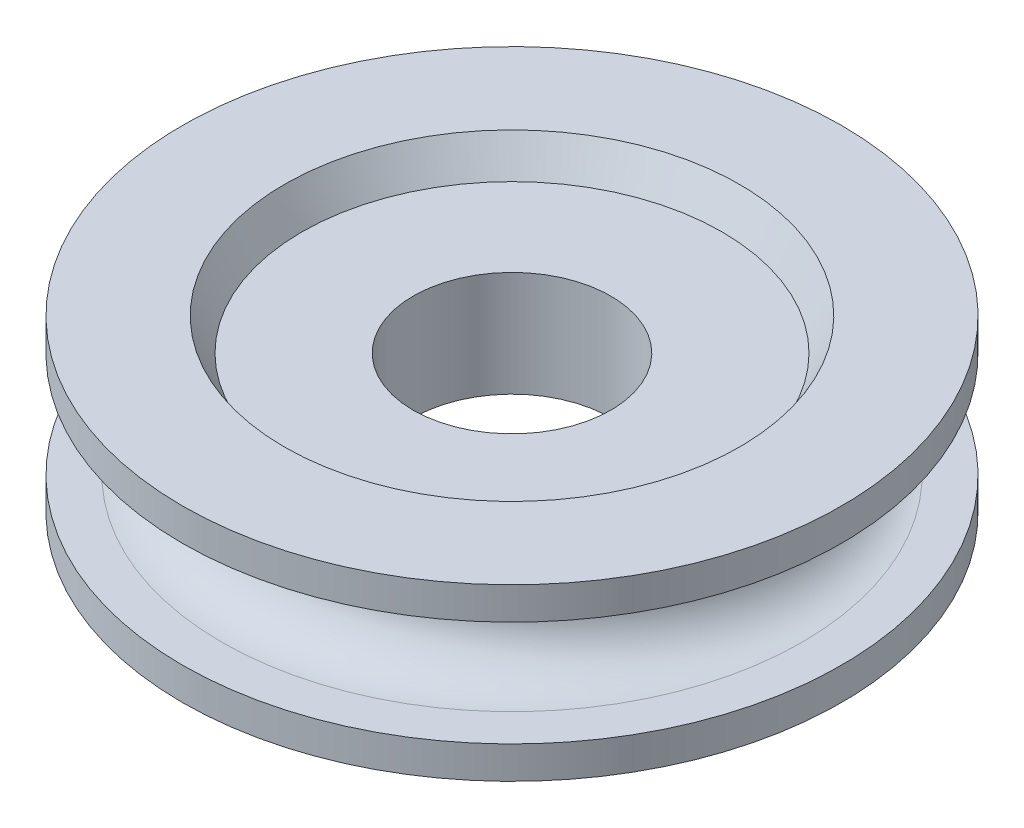
SolidWorks part; units mm, degrees
ref_plane "Спереди" through (0, 0, 0) normal (0, 0, 1) x (1, 0, 0)
ref_plane "Сверху" through (0, 0, 0) normal (0, 1, 0) x (1, 0, 0)
ref_plane "Справа" through (0, 0, 0) normal (1, 0, 0) x (0, 0, -1)
sketch "Эскиз1" plane through (0, 0, 0) normal (0, 0, 1) x (1, 0, 0)
  line L0 (7.5, 4) -> (7.5, -4)
  line L1 (7.5, -4) -> (15.9329, -4)
  line L2 (15.9329, -4) -> (17.261, -6.4591)
  line L3 (17.261, -6.4591) -> (25, -6.4591)
  line L4 (-50.7153, 0) -> (148.2535, 0) construction
  line L6 (17.261, 6.4591) -> (25, 6.4591)
  line L7 (15.9329, 4) -> (17.261, 6.4591)
  line L9 (7.5, 4) -> (15.9329, 4)
  line L10 (0, 40.9325) -> (0, -32.1466) construction
  line L11 (22, 4) -> (25, 4)
  line L12 (25, 4) -> (25, 6.4591)
  line L13 (22, -4) -> (25, -4)
  line L14 (25, -4) -> (25, -6.4591)
  arc A1 (22, 4) -> (22, -4) centre (22, 0) ccw
  point P13 (7.5, 0)
  point P15 (7.5, 0)
  point P16 (31.0789, 0)
  point P21 (27.926, 0)
  point P22 (24.5028, 0)
revolve "Повернуть1" add sketch "Эскиз1" angle 360 about L10
